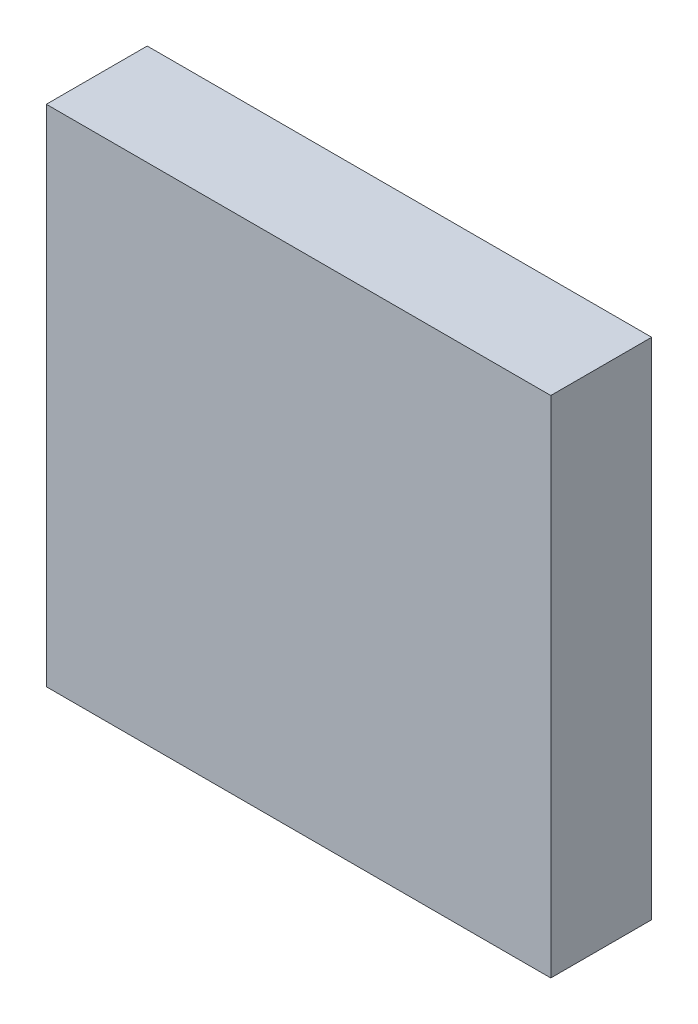
SolidWorks part; units mm, degrees
ref_plane "Front Plane" through (0, 0, 0) normal (0, 0, 1) x (1, 0, 0)
ref_plane "Top Plane" through (0, 0, 0) normal (0, 1, 0) x (1, 0, 0)
ref_plane "Right Plane" through (0, 0, 0) normal (1, 0, 0) x (0, 0, -1)
sketch "Sketch2" plane through (0, 0, 0) normal (0, 0, 1) x (1, 0, 0)
  line L1 (15, 15) -> (-15, 15)
  line L2 (15, 15) -> (15, -15)
  line L3 (15, -15) -> (-15, -15)
  line L4 (-15, 15) -> (-15, -15)
  line L5 (15, 15) -> (-15, -15) construction
  line L6 (15, -15) -> (-15, 15) construction
  circle A0 centre (0, 0) radius 12.55
  point P7 (0, 0)
  dimension "D1" = 25.1
  dimension "D2" = 30
  dimension "D3" = 30
extrude "Boss-Extrude1" add sketch "Sketch2" against normal blind 5
sketch "Sketch4" plane through (0, 0, 0) normal (0, 0, 1) x (1, 0, 0)
  line L1 (-15, 15) -> (15, 15)
  line L2 (-15, 15) -> (-15, -15)
  line L3 (-15, -15) -> (15, -15)
  line L4 (15, 15) -> (15, -15)
  line L5 (-15, 15) -> (15, -15) construction
  line L6 (-15, -15) -> (15, 15) construction
  point P0 (0, 0)
extrude "Boss-Extrude2" add sketch "Sketch4" along normal blind 1
